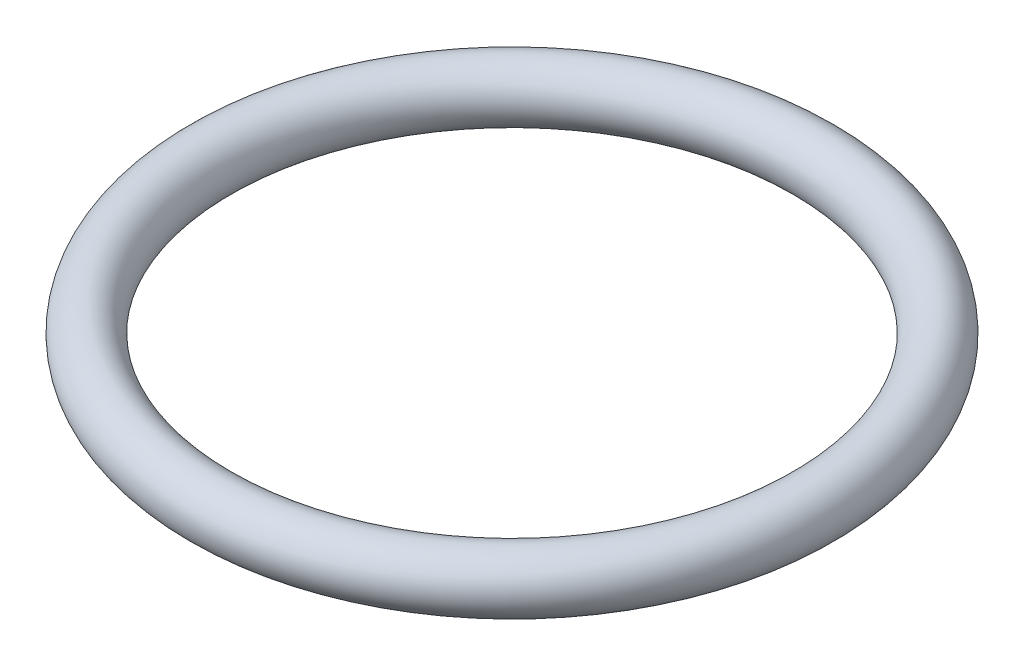
SolidWorks part; units mm, degrees
ref_plane "Plan de face" through (0, 0, 0) normal (0, 0, 1) x (1, 0, 0)
ref_plane "Plan de dessus" through (0, 0, 0) normal (0, 1, 0) x (1, 0, 0)
ref_plane "Plan de droite" through (0, 0, 0) normal (1, 0, 0) x (0, 0, -1)
ref_axis "Axe2" through (0, 9.5442, 0) along (0, -1, 0)
sketch "Esquisse1" plane through (0, 0, 0) normal (0, 0, 1) x (1, 0, 0)
  circle A0 centre (13.81, 0) radius 1.31
  dimension "D1" = 2.62
  dimension "D2" = 13.81
revolve "Révolution1" add sketch "Esquisse1" angle 360 about axis through (0, 9.5442, 0) along (0, -1, 0)
